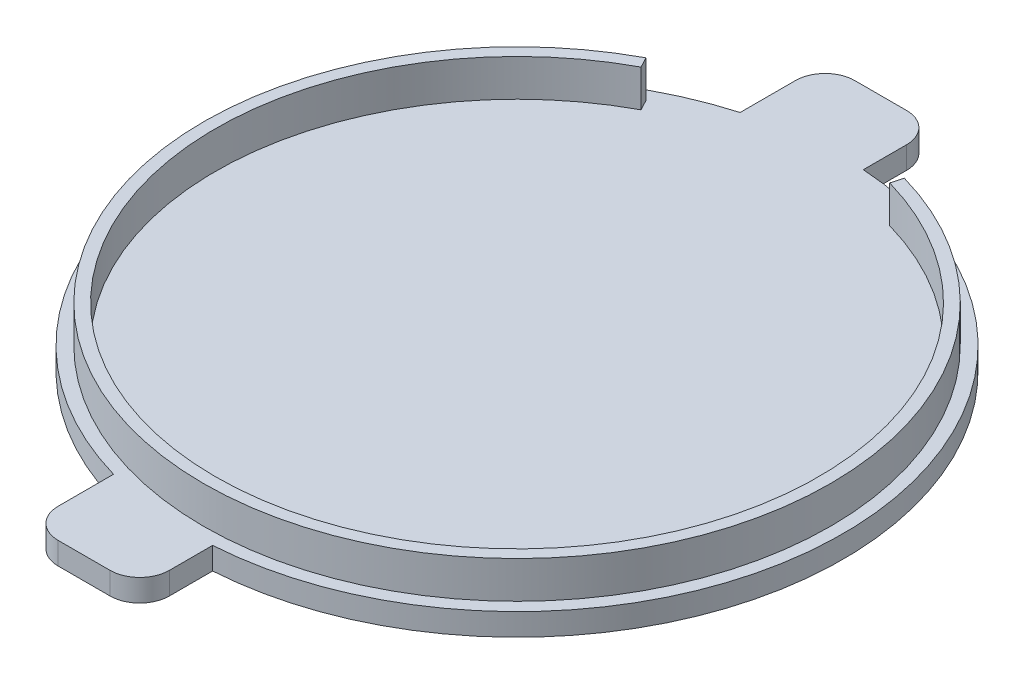
SolidWorks part; units mm, degrees
ref_plane "Front Plane" through (0, 0, 0) normal (0, 0, 1) x (1, 0, 0)
ref_plane "Top Plane" through (0, 0, 0) normal (0, 1, 0) x (1, 0, 0)
ref_plane "Right Plane" through (0, 0, 0) normal (1, 0, 0) x (0, 0, -1)
sketch "Sketch1" plane through (0, 0, 0) normal (0, 1, 0) x (1, 0, 0)
  circle A0 centre (0, 0) radius 44
  dimension "D1" = 88
extrude "Boss-Extrude1" add sketch "Sketch1" along normal blind 3 contours A0
sketch "Sketch2" plane through (0, 3, 0) normal (0, 1, 0) x (1, 0, 0)
  line L0 (0, 0) -> (-19.9219, 37.315) construction
  line L1 (0, 0) -> (11.5905, 40.6811) construction
  line L2 (-19.1684, 35.9035) -> (-19.9219, 37.315)
  line L3 (11.1521, 39.1423) -> (11.5905, 40.6811)
  arc A0 (-19.1684, 35.9035) -> (11.1521, 39.1423) centre (0, 0) ccw
  arc A1 (-19.9219, 37.315) -> (11.5905, 40.6811) centre (0, 0) ccw
  circle A2 centre (0, 0) radius 44 construction
  dimension "D1" = 81.4
  dimension "D2" = 84.6
  dimension "D3" = 44
extrude "Boss-Extrude2" add sketch "Sketch2" along normal blind 5
sketch "Sketch3" plane through (0, 0, 0) normal (0, -1, 0) x (1, 0, 0)
  line L0 (0, 0) -> (-4.6734, -43.7511) construction
  line L1 (-19.1684, -35.9035) -> (-19.9219, -37.315) construction
  line L6 (11.5905, -40.6811) -> (11.1521, -39.1423) construction
  line L16 (-1.1734, -53.7511) -> (-8.1734, -53.7511)
  line L17 (2.8266, -49.7511) -> (2.8266, -33.7511)
  line L18 (2.8266, -33.7511) -> (-12.1734, -33.7511)
  line L19 (-12.1734, -49.7511) -> (-12.1734, -33.7511)
  line L20 (2.8266, -53.7511) -> (-12.1734, -33.7511) construction
  line L21 (2.8266, -33.7511) -> (-12.1734, -53.7511) construction
  circle A4 centre (0, 0) radius 44 construction
  arc A5 (2.8266, -49.7511) -> (-1.1734, -53.7511) centre (-1.1734, -49.7511) cw
  arc A6 (-12.1734, -49.7511) -> (-8.1734, -53.7511) centre (-8.1734, -49.7511) ccw
  dimension "D1" = 20
  dimension "D2" = 15
  dimension "D3" = 4
  dimension "D4" = 4
extrude "Boss-Extrude3" add sketch "Sketch3" against normal up to surface (3 mm away) contours L16 A6 L19 L18 L17 A5 up to face at (0, 3, 44)
mirror "Mirror1" about plane through (0, 0, 0) normal (0, 0, 1) of "Boss-Extrude3"
